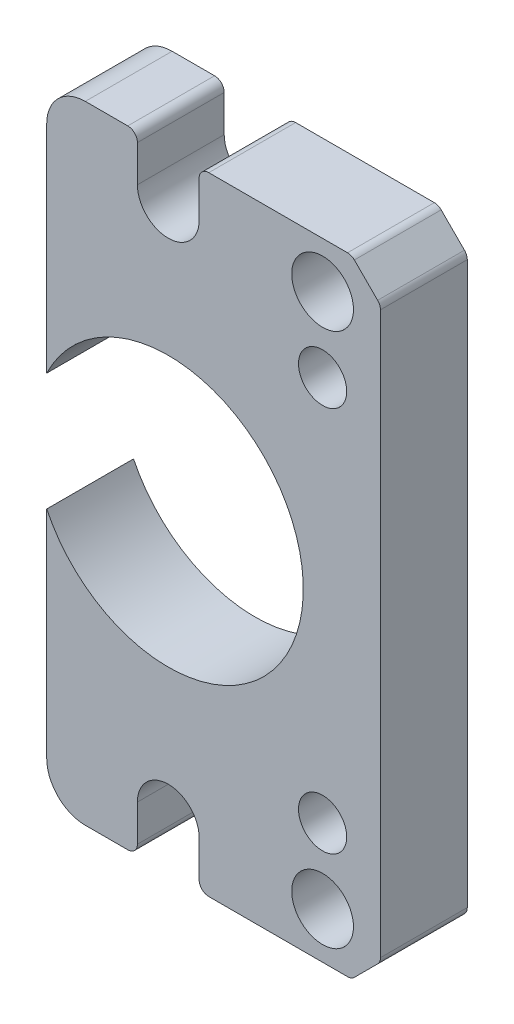
SolidWorks part; units mm, degrees
material "Liga de aço"
ref_plane "Plano frontal" through (0, 0, 0) normal (0, 0, 1) x (1, 0, 0)
ref_plane "Plano superior" through (0, 0, 0) normal (0, 1, 0) x (1, 0, 0)
ref_plane "Plano direito" through (0, 0, 0) normal (1, 0, 0) x (0, 0, -1)
ref_plane "Plano1" through (0, 0, -4.5) normal (0, 0, -1) x (-1, 0, 0)
sketch "Esboço1" plane through (0, 0, -4.5) normal (0, 0, -1) x (-1, 0, 0)
  line L0 (-10.8536, -14.8964) -> (-9.6464, -16.1036)
  line L1 (-9.2929, -16.25) -> (-2.1, -16.25)
  line L2 (-1.6, -15.75) -> (-1.6, -13.8564)
  line L3 (1.6, -13.8564) -> (1.6, -15.75)
  line L4 (2.1, -16.25) -> (9.2929, -16.25)
  line L5 (9.6464, -16.1036) -> (10.8536, -14.8964)
  line L6 (11, -14.5429) -> (11, 14.5429)
  line L7 (10.8536, 14.8964) -> (9.6464, 16.1036)
  line L8 (9.2929, 16.25) -> (2.1, 16.25)
  line L9 (1.6, 15.75) -> (1.6, 13.8564)
  line L10 (-1.6, 13.8564) -> (-1.6, 15.75)
  line L11 (-2.1, 16.25) -> (-9.2929, 16.25)
  line L12 (-9.6464, 16.1036) -> (-10.8536, 14.8964)
  line L13 (-11, 14.5429) -> (-11, -14.5429)
  arc A0 (-9.6464, -16.1036) -> (-9.2929, -16.25) centre (-9.2929, -15.75) ccw
  arc A1 (-2.1, -16.25) -> (-1.6, -15.75) centre (-2.1, -15.75) ccw
  arc A2 (-1.6, -13.8564) -> (1.6, -13.8564) centre (0, -13.8564) cw
  arc A3 (1.6, -15.75) -> (2.1, -16.25) centre (2.1, -15.75) ccw
  arc A4 (9.2929, -16.25) -> (9.6464, -16.1036) centre (9.2929, -15.75) ccw
  arc A5 (10.8536, -14.8964) -> (11, -14.5429) centre (10.5, -14.5429) ccw
  arc A6 (11, 14.5429) -> (10.8536, 14.8964) centre (10.5, 14.5429) ccw
  arc A7 (9.6464, 16.1036) -> (9.2929, 16.25) centre (9.2929, 15.75) ccw
  arc A8 (2.1, 16.25) -> (1.6, 15.75) centre (2.1, 15.75) ccw
  arc A9 (1.6, 13.8564) -> (-1.6, 13.8564) centre (0, 13.8564) cw
  arc A10 (-1.6, 15.75) -> (-2.1, 16.25) centre (-2.1, 15.75) ccw
  arc A11 (-9.2929, 16.25) -> (-9.6464, 16.1036) centre (-9.2929, 15.75) ccw
  arc A12 (-10.8536, 14.8964) -> (-11, 14.5429) centre (-10.5, 14.5429) ccw
  arc A13 (-11, -14.5429) -> (-10.8536, -14.8964) centre (-10.5, -14.5429) ccw
  circle A14 centre (-8, -10) radius 1.25
  circle A15 centre (8, -10) radius 1.25
  circle A16 centre (8, 10) radius 1.25
  circle A17 centre (-8, 10) radius 1.25
  circle A18 centre (-8, -13.8564) radius 1.6
  circle A19 centre (8, -13.8564) radius 1.6
  circle A20 centre (8, 13.8564) radius 1.6
  circle A21 centre (-8, 13.8564) radius 1.6
  circle A22 centre (0, 0) radius 7
extrude "Ressalto-extrusão1" add sketch "Esboço1" against normal blind 4.5
sketch "Esboço2" plane through (0, 0, 0) normal (0, 0, 1) x (1, 0, 0)
  line L0 (-15.3837, -16.25) -> (-6.3009, -16.25)
  line L1 (-15.3837, -16.25) -> (-15.3837, 16.25)
  line L2 (-15.3837, 16.25) -> (-6.3009, 16.25)
  line L3 (-6.3009, -16.25) -> (-6.3009, 16.25)
  line L4 (-15.3837, -16.25) -> (-6.3009, 16.25) construction
  line L5 (-15.3837, 16.25) -> (-6.3009, -16.25) construction
  line L6 (-9.2929, 16.25) -> (-2.1, 16.25) construction
  line L7 (-2.1, -16.25) -> (-9.2929, -16.25) construction
extrude "Corte-extrusão1" cut sketch "Esboço2" against normal through all
fillet "Filete1" radius 2 2 edges at (-6.3009, -16.25, -2.25) (-6.3009, 16.25, -2.25)
